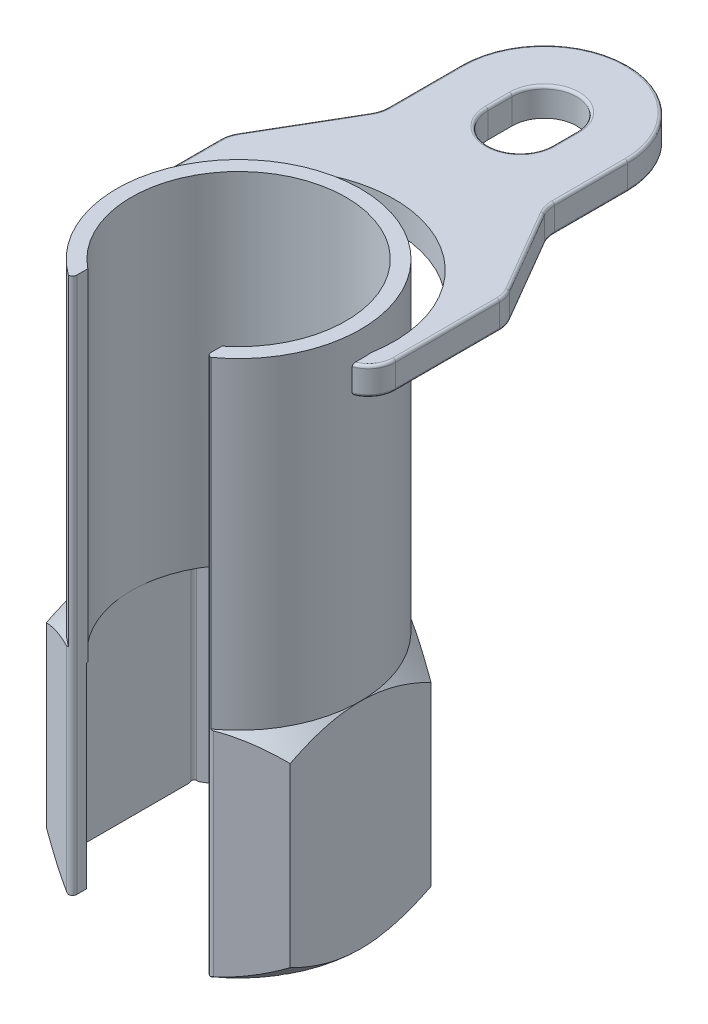
SolidWorks part; units mm, degrees
ref_plane "Front" through (0, 0, 0) normal (0, 0, 1) x (1, 0, 0)
ref_plane "Top" through (0, 0, 0) normal (0, 1, 0) x (1, 0, 0)
ref_plane "Right" through (0, 0, 0) normal (1, 0, 0) x (0, 0, -1)
sketch "Sketch1" plane through (0, 0, 0) normal (0, 1, 0) x (1, 0, 0)
  line L0 (-12.5, -15.6125) -> (-12.5, -19.0331)
  line L1 (0, 26.25) -> (-22.7332, 13.125)
  line L2 (0, 11.9615) -> (0, -7.933) construction
  line L3 (-22.7332, 13.125) -> (-22.7332, -13.125)
  line L4 (-22.7332, -13.125) -> (-12.5, -19.0331)
  line L5 (12.5, -19.0331) -> (22.7332, -13.125)
  line L6 (22.7332, -13.125) -> (22.7332, 13.125)
  line L7 (22.7332, 13.125) -> (0, 26.25)
  line L8 (12.5, -15.6125) -> (12.5, -19.0331)
  arc A0 (12.5, -18.9881) -> (-12.5, -18.9881) centre (0, 0) ccw construction
  arc A1 (12.5, -15.6125) -> (-12.5, -15.6125) centre (0, 0) ccw
  point P18 (-22.7332, -13.125)
  point P26 (22.7332, 13.125)
  dimension "D" = 52.5
  dimension "D2" = 40
  dimension "C" = 25
extrude "Extrude1" add sketch "Sketch1" along normal blind 40
sketch "Sketch3" plane through (0, 40, 0) normal (0, 1, 0) x (-1, 0, 0)
  line L0 (-22.7332, 13.125) -> (-22.7332, -13.125) construction
  line L2 (-12.5, 18.988) -> (-12.5, 15.6125)
  line L3 (12.5, 18.988) -> (12.5, 15.6125)
  arc A0 (-12.5, 15.6125) -> (12.5, 15.6125) centre (0, 0) ccw
  arc A1 (-12.5, 15.6125) -> (12.5, 15.6125) centre (0, 0) ccw construction
  arc A2 (-12.5, 18.988) -> (12.5, 18.988) centre (0, 0) ccw
  dimension "D1" = 0.0001
extrude "Extrude2" add sketch "Sketch3" along normal blind 60
sketch "Sketch8" plane through (0, 0, 0) normal (0, -1, 0) x (1, 0, 0)
  line L1 (22.7332, 13.125) -> (22.7332, -13.125) construction
  circle A0 centre (0, 0) radius 22.7332
extrude "Cut-Extrude4" cut sketch "Sketch8" against normal through all draft 45 flip side to cut
sketch "Sketch19" plane through (0, 40, 0) normal (0, 1, 0) x (-1, 0, 0)
  circle A1 centre (0, 0) radius 22.7331
  arc A2 (-12.5, 18.988) -> (12.5, 18.988) centre (0, 0) ccw construction
extrude "Cut-Extrude6" cut sketch "Sketch19" against normal through all draft 45 flip side to cut
sketch "Sketch26" plane through (0, 0, 0) normal (0, -1, 0) x (1, 0, 0)
  line L1 (-20, -11.547) -> (0, -23.094)
  line L2 (0, -23.094) -> (20, -11.547)
  line L3 (20, -11.547) -> (20, 11.547)
  line L4 (20, 11.547) -> (0, 23.094)
  line L5 (0, 23.094) -> (-20, 11.547)
  line L6 (-20, 11.547) -> (-20, -11.547)
  circle A0 centre (0, 0) radius 20 construction
  dimension "D1" = 40
extrude "Cut-Extrude9" cut sketch "Sketch26" against normal up to vertex (38.5 mm away)
fillet "Fillet1" radius 0.8 7 edges at (-20, 18.422, -11.547) (-20, 18.422, 11.547) (20, 18.422, 11.547) (20, 18.422, -11.547) (-12.5, 19.9999, 19.0331) (12.5, 19.9999, 19.0331) (0, 18.422, -23.094)
sketch "Sketch4" [suppressed] plane through (0, 0, 0) normal (0, 1, 0) x (-1, 0, 0)
  line L0 (0, -11.2014) -> (0, 12.8888) construction
  line L1 (-10, -2.5) -> (10, -2.5)
  line L2 (-10, -2.5) -> (-10, 3.8)
  line L3 (-10, 3.8) -> (10, 3.8)
  line L4 (10, -2.5) -> (10, 3.8)
  line L5 (16.2585, 0) -> (-21.4153, 0) construction
  dimension "D1" = 40
  dimension "D2" = 7
  dimension "D3" = 5.7
sketch "Sketch12" [suppressed] plane through (0, 0, 0) normal (0, 1, 0) x (1, 0, 0)
  line L0 (-11, -4) -> (11, -4)
  line L1 (0, 0) -> (-11.4274, 0) construction
  line L2 (-11, 2.7) -> (11, 2.7)
  line L3 (-4.5, 14.3091) -> (4.5, 14.3091)
  line L4 (-7, 3.2909) -> (-7, -3.2909) construction
  line L5 (7, -3.2909) -> (7, 3.2909) construction
  arc A0 (-11, -4) -> (11, -4) centre (0, 0) ccw
  arc A1 (-6.3246, -3) -> (6.3246, -3) centre (0, 0) ccw construction
  arc A2 (-4.5, 14.3091) -> (-11, 2.7) centre (2.617, 2.7) ccw
  arc A3 (-4.5, 14.3091) -> (4.5, 14.3091) centre (0, 0) ccw construction
  arc A4 (4.5, 14.3091) -> (11, 2.7) centre (-2.617, 2.7) cw
ref_plane "Plane3" through (0, 90, 0) normal (0, 1, 0) x (-1, 0, 0)
sketch "Sketch16" plane through (0, 90, 0) normal (0, 1, 0) x (-1, 0, 0)
  line L5 (0, 0) -> (0, 54.2988) construction
  line L6 (-15.5, -57) -> (-15.5, -43.3788)
  line L10 (15.5, -43.3788) -> (15.5, -57)
  line L11 (25.3053, -25.191) -> (16.1947, -40.809)
  line L12 (-25.3053, -25.191) -> (-16.1947, -40.809)
  line L13 (-26, -3.278) -> (-26, -22.6212)
  line L14 (26, -3.278) -> (26, -22.6212)
  line L15 (38.3763, 1.5) -> (-38.1367, 1.5) construction
  arc A0 (-13.2849, 18.4473) -> (13.2849, 18.4473) centre (0, 0) ccw construction
  arc A1 (-22.6835, 1.5) -> (22.6835, 1.5) centre (0, 0) ccw
  arc A2 (26, -3.278) -> (22.6835, 1.5) centre (20.9, -3.278) ccw
  arc A3 (-26, -3.278) -> (-22.6835, 1.5) centre (-20.9, -3.278) cw
  arc A4 (-26, -22.6212) -> (-25.3053, -25.191) centre (-20.9, -22.6212) ccw
  arc A5 (-16.1947, -40.809) -> (-15.5, -43.3788) centre (-20.6, -43.3788) cw
  arc A7 (26, -22.6212) -> (25.3053, -25.191) centre (20.9, -22.6212) cw
  arc A8 (16.1947, -40.809) -> (15.5, -43.3788) centre (20.6, -43.3788) ccw
  arc A15 (15.5, -57) -> (-15.5, -57) centre (0, -57) cw
  point P18 (-26, -24)
  point P22 (-15.5, -42)
  point P25 (26, -24)
  point P30 (15.5, -42)
  dimension "D1" = 52
  dimension "D2" = 24
  dimension "D3" = 42
  dimension "D4" = 5.1
  dimension "D6" = 31
  dimension "D7" = 57
  dimension "D14" = 1.5
extrude "Extrude7" add sketch "Sketch16" along normal blind 5.2
sketch "Sketch25" plane through (0, 95.2, 0) normal (0, -1, 0) x (1, 0, 0)
  line L1 (-29.4486, 0) -> (37.9585, 0) construction
  line L3 (0, -57.3769) -> (0, 10.8445) construction
  line L4 (-6, -57) -> (-6, -52.5)
  line L5 (6, -57) -> (6, -52.5)
  arc A0 (-13.2849, 18.4473) -> (13.2849, 18.4473) centre (0, 0) ccw construction
  arc A2 (-15.5, -57) -> (15.5, -57) centre (0, -57) ccw construction
  arc A6 (22.6449, -2) -> (-22.6449, -2) centre (0, 0) cw
  arc A7 (22.6449, -2) -> (-22.6449, -2) centre (0, -6) cw
  arc A8 (6, -57) -> (-6, -57) centre (0, -57) cw
  arc A9 (6, -52.5) -> (-6, -52.5) centre (0, -52.5) ccw
  dimension "D1" = 20
  dimension "D2" = 12
  dimension "D3" = 2
  dimension "D4" = 6
extrude "Cut-Extrude8" cut sketch "Sketch25" along normal up to next
fillet "Fillet4" radius 0.5 30 edges at (6, 95.2, -54.75) (0, 95.2, -63) (-6, 95.2, -54.75) (25.0896, 95.2, -0.3699) (26, 95.2, -12.9496) (25.8233, 95.2, -23.9522) (-25.0896, 95.2, -0.3699) (-26, 95.2, -12.9496) (-25.8233, 95.2, -23.9522) (-20.75, 95.2, -33) (-15.6767, 95.2, -42.0478) (-15.5, 95.2, -50.1894) (0, 95.2, -72.5) (15.5, 95.2, -50.1894) (15.6767, 95.2, -42.0478) (25.0896, 90, -0.3699) (26, 90, -12.9496) (25.8233, 90, -23.9522) (-25.0896, 90, -0.3699) (-26, 90, -12.9496) (-25.8233, 90, -23.9522) (-20.75, 90, -33) (-15.6767, 90, -42.0478) (-15.5, 90, -50.1894) (0, 90, -72.5) (15.5, 90, -50.1894) (15.6767, 90, -42.0478) (0, 95.2, -46.5) (20.75, 95.2, -33) (20.75, 90, -33)
sketch "Sketch20" [suppressed] plane through (0, 0, 0) normal (0, 1, 0) x (1, 0, 0)
  line L0 (0, 0) -> (0, 12.8849) construction
  line L1 (-7.5, -9.3675) -> (-7.5, -14.4157)
  line L2 (7.5, -9.3675) -> (7.5, -14.4157)
  arc A0 (7.5, -14.4157) -> (-7.5, -14.4157) centre (0, 0) ccw
  arc A1 (7.5, -9.3675) -> (-7.5, -9.3675) centre (0, 0) ccw
  circle A2 centre (0, 0) radius 16.25 construction
  circle A3 centre (0, 0) radius 12 construction
  dimension "D1" = 52.5
  dimension "D2" = 40
  dimension "D3" = 25
extrude "Extrude3" [suppressed] add sketch "Sketch20" along normal blind 52
ref_plane "Plane7" [suppressed] through (0, 41.999, 0) normal (0, 1, 0) x (-1, 0, 0)
sketch "Sketch21" [suppressed] plane through (0, 41.999, 0) normal (0, 1, 0) x (-1, 0, 0)
  line L1 (2.5, 16.0565) -> (2.5, 19.8734)
  line L2 (7.5, 14.4157) -> (7.5, 9.3675) construction
  line L4 (7.5, 14.4157) -> (7.5, 18.5729)
  arc A1 (2.5, 16.0565) -> (7.5, 14.4157) centre (0, 0) ccw
  arc A2 (2.5, 19.8734) -> (7.5, 18.5729) centre (0, 0) ccw
  arc A3 (-7.5, 14.4157) -> (7.5, 14.4157) centre (0, 0) ccw construction
  dimension "D1" = 4.68
  dimension "D2" = 2.5
extrude "Extrude4" [suppressed] add sketch "Sketch21" against normal blind 15.5 separate body
ref_plane "Plane6" [suppressed] through (5.0421, 41.999, -19.385) normal (0.2517, 0, -0.9678) x (-0.9678, 0, -0.2517)
sketch "Sketch22" [suppressed] plane through (5.0421, 41.999, -19.385) normal (0.2517, 0, -0.9678) x (-0.9678, 0, -0.2517)
  line L0 (20.03, 0) -> (-20.03, 0) construction
  line L1 (0, 0) -> (0, 14.8678) construction
  line L2 (-3.2, -3.3) -> (3.2, -3.3)
  line L3 (-3.2, -3.3) -> (-3.2, -9.7)
  line L4 (-3.2, -9.7) -> (3.2, -9.7)
  line L5 (3.2, -3.3) -> (3.2, -9.7)
  line L7 (-18.9345, -6.5) -> (19.4735, -6.5) construction
  dimension "D1" = 8.4
  dimension "D2" = 7.75
  dimension "D3" = 8.4
extrude "Extrude5" [suppressed] add sketch "Sketch22" along normal blind 17 and the other way up to next
sketch "Sketch23" [suppressed] plane through (8.0628, 0, -30.9986) normal (0.2517, 0, -0.9678) x (-0.9678, 0, -0.2517)
  circle A0 centre (0, 35.499) radius 4.5255
extrude "Extrude6" [suppressed] add sketch "Sketch23" along normal blind 42 draft 2
dome "Dome1" [suppressed] faces to dome 1 distance 3 parameters "D1"=3
sketch "Sketch24" [suppressed] plane through (0, 0, 0) normal (0, -1, 0) x (1, 0, 0)
  line L2 (-12, 6.9282) -> (-12, -6.9282)
  line L3 (-12, -6.9282) -> (0, -13.8564)
  line L4 (0, -13.8564) -> (12, -6.9282)
  line L5 (12, -6.9282) -> (12, 6.9282)
  line L6 (12, 6.9282) -> (0, 13.8564)
  line L7 (0, 13.8564) -> (-12, 6.9282)
  circle A0 centre (0, 0) radius 12 construction
  dimension "D1" = 40
extrude "Cut-Extrude7" [suppressed] cut sketch "Sketch24" against normal through all
fillet "Fillet2" [suppressed] radius 0.5
fillet "Fillet3" [suppressed] radius 0.5
fillet "Fillet5" [suppressed] radius 1
